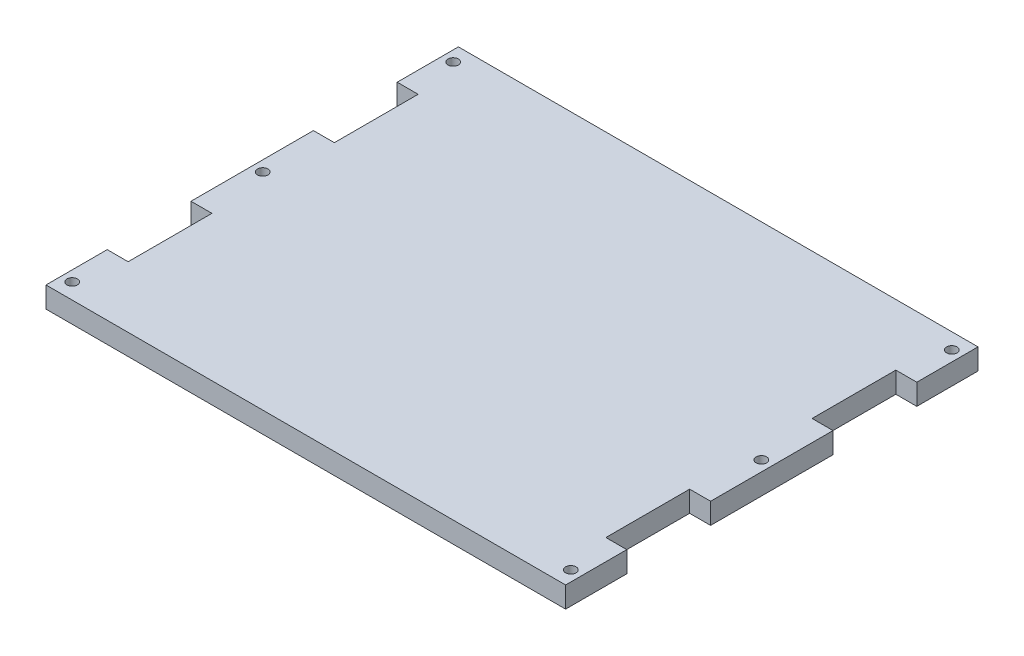
SolidWorks part; units mm, degrees
ref_plane "Alzado" through (0, 0, 0) normal (0, 0, 1) x (1, 0, 0)
ref_plane "Planta" through (0, 0, 0) normal (0, 1, 0) x (1, 0, 0)
ref_plane "Vista lateral" through (0, 0, 0) normal (1, 0, 0) x (0, 0, -1)
sketch "Croquis1" plane through (0, 0, 0) normal (0, 1, 0) x (1, 0, 0)
  line L0 (0, 125) -> (0, -125) construction
  line L1 (-157.5, -125) -> (157.5, -125)
  line L2 (-157.5, -125) -> (-157.5, 125)
  line L3 (-157.5, 125) -> (157.5, 125)
  line L4 (157.5, -125) -> (157.5, 125)
  line L5 (-157.5, -125) -> (157.5, 125) construction
  line L6 (-157.5, 125) -> (157.5, -125) construction
  line L7 (-151.15, 125) -> (-151.15, -125) construction
  circle A0 centre (-151.15, -115.475) radius 3.175
  circle A1 centre (-151.15, 0) radius 3.175
  circle A2 centre (-151.15, 115.475) radius 3.175
  circle A3 centre (151.15, 115.475) radius 3.175
  circle A4 centre (151.15, 0) radius 3.175
  circle A5 centre (151.15, -115.475) radius 3.175
  point P0 (0, 0)
  dimension "D4" = 6.35
  dimension "D5" = 9.525
  dimension "D6" = 6.35
  dimension "D7" = 6.35
  dimension "D8" = 9.525
  dimension "D1" = 315
  dimension "D2" = 250
  dimension "D3" = 6.35
extrude "Saliente-Extruir1" add sketch "Croquis1" along normal blind 12.7
sketch "Croquis2" plane through (0, 12.7, 0) normal (0, 1, 0) x (1, 0, 0)
  line L0 (-157.5, 125) -> (-157.5, -125) construction
  line L1 (-157.5, 87.9) -> (-144.8, 87.9)
  line L2 (-157.5, 87.9) -> (-157.5, 37.1)
  line L3 (-157.5, 37.1) -> (-144.8, 37.1)
  line L4 (-144.8, 87.9) -> (-144.8, 37.1)
  line L5 (0, 0) -> (-157.5, 0) construction
  line L6 (0, 0) -> (0, 125) construction
  line L7 (157.5, 125) -> (-157.5, 125) construction
  line L8 (-157.5, -87.9) -> (-144.8, -87.9)
  line L9 (-157.5, -87.9) -> (-157.5, -37.1)
  line L10 (-157.5, -37.1) -> (-144.8, -37.1)
  line L11 (-144.8, -87.9) -> (-144.8, -37.1)
  circle A0 centre (-151.15, 115.475) radius 3.175 construction
  point P8 (-144.8, 62.5)
  dimension "D3" = 52.975
  dimension "D1" = 50.8
  dimension "D2" = 12.7
extrude "Cortar-Extruir1" cut sketch "Croquis2" against normal through all
mirror "Simetría1" about plane through (0, 0, 0) normal (1, 0, 0) of "Cortar-Extruir1"
sketch "Croquis3" plane through (0, 0, 0) normal (0, -1, 0) x (-1, 0, 0)
  line L0 (157.5, -125) -> (104.5, -63) construction
  line L1 (157.5, -87.8) -> (157.5, -37.2) construction
  line L2 (157.5, -125) -> (-157.5, -125) construction
  circle A0 centre (104.5, -63) radius 5
  dimension "D3" = 10
  dimension "D1" = 53
  dimension "D2" = 62
extrude "Cortar-Extruir2" cut sketch "Croquis3" against normal blind 1
